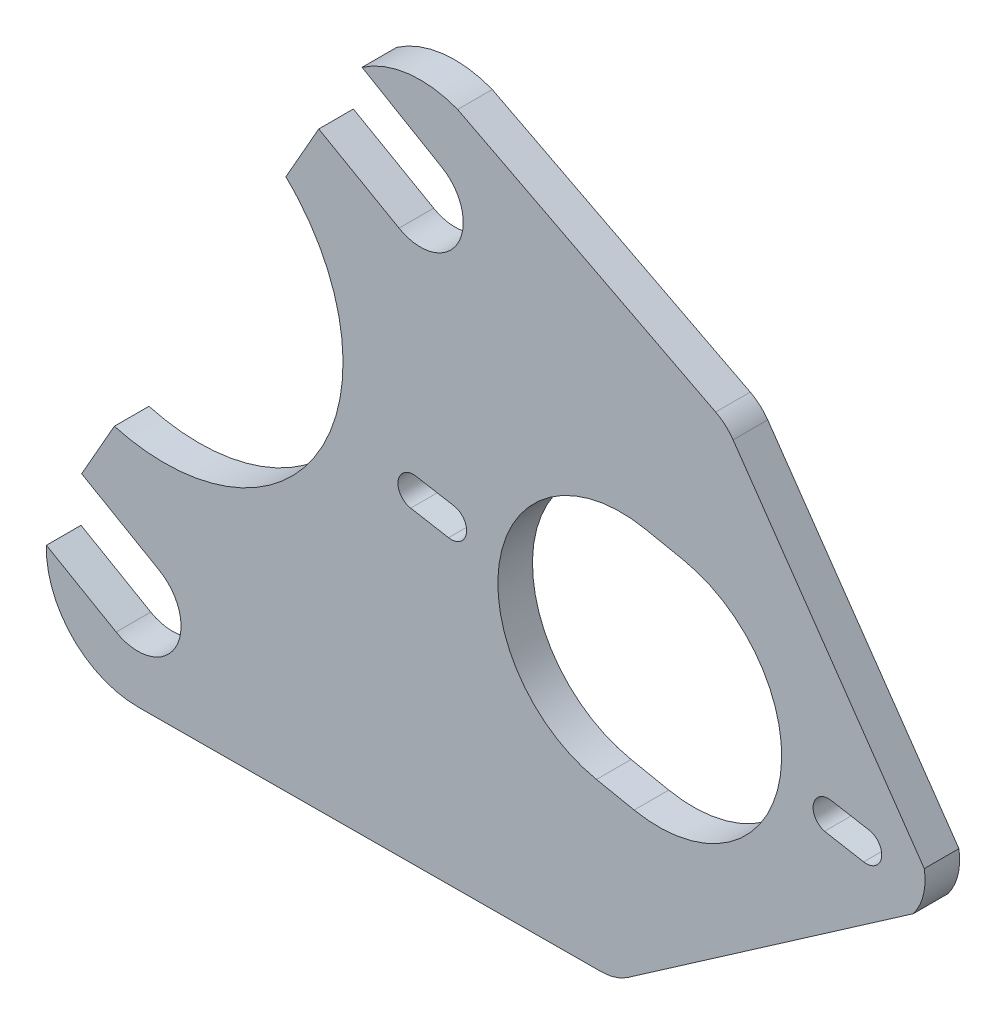
SolidWorks part; units mm, degrees
ref_plane "Front Plane" through (0, 0, 0) normal (0, 0, 1) x (1, 0, 0)
ref_plane "Top Plane" through (0, 0, 0) normal (0, 1, 0) x (1, 0, 0)
ref_plane "Right Plane" through (0, 0, 0) normal (1, 0, 0) x (0, 0, -1)
sketch "Model" plane through (0, 0, 0) normal (0, 0, 1) x (1, 0, 0)
  line L0 (135.7866, 62.5287) -> (131.8474, 63.2232)
  line L1 (59.7829, 35.593) -> (65.7308, 35.6231)
  line L2 (78.5552, 97.0562) -> (86.904, 92.2982)
  line L4 (83.0608, 104.8605) -> (91.3561, 100.0093)
  line L5 (75.135, 91.0384) -> (78.5552, 97.0562)
  line L6 (61.9848, 49.0002) -> (53.897, 53.6704)
  line L7 (53.897, 53.6704) -> (57.2951, 59.6494)
  line L8 (50.2285, 45.3956) -> (57.481, 41.2084)
  line L9 (107.8791, 35.8363) -> (113.8271, 35.8664)
  line L10 (65.7308, 35.6231) -> (107.8791, 35.8363)
  line L11 (116.4435, 77.205) -> (112.5231, 77.9992)
  line L12 (135.2289, 59.3776) -> (131.1616, 60.1004)
  line L13 (92.6109, 70.1416) -> (88.6717, 70.8362)
  line L14 (92.0552, 66.9902) -> (88.116, 67.6848)
  line L15 (111.3606, 52.1146) -> (107.4403, 52.9088)
  line L16 (143.1744, 59.6379) -> (139.0962, 35.8664)
  line L17 (113.8271, 35.8664) -> (139.0962, 35.8664)
  line L18 (92.9995, 106.0361) -> (143.1744, 59.6379)
  arc A0 (57.481, 41.2084) -> (61.9848, 49.0002) centre (59.7329, 45.1043) ccw
  arc A1 (86.904, 92.2982) -> (91.3561, 100.0093) centre (89.13, 96.1538) ccw
  arc A2 (111.3606, 52.1146) -> (116.4435, 77.205) centre (113.9021, 64.6598) ccw
  arc A4 (92.9995, 106.0361) -> (83.0608, 104.8605) centre (89.1296, 96.154) ccw
  arc A5 (50.2285, 45.3956) -> (59.7829, 35.593) centre (59.7348, 45.1036) ccw
  arc A6 (112.5231, 77.9992) -> (107.4403, 52.9088) centre (109.9817, 65.454) ccw
  arc A7 (131.8474, 63.2232) -> (131.4196, 60.0545) centre (131.5696, 61.6475) ccw
  arc A8 (88.729, 70.825) -> (88.116, 67.6848) centre (88.3938, 69.2605) ccw
  arc A9 (92.0552, 66.9902) -> (92.6109, 70.1416) centre (92.3331, 68.5659) ccw
  arc A10 (135.2289, 59.3776) -> (135.7866, 62.5287) centre (135.5088, 60.953) ccw
  ellipse E1 centre (62.0385, 77.7176) end of major axis (78.7041, 68.2458) minor radius 18.6473 (57.2951, 59.6494) -> (75.135, 91.0384) ccw
  point P42 (106.1748, 87.0422)
  point P43 (131.5661, 69.2597)
  point P44 (113.7866, 43.8663)
  point P45 (88.3952, 61.6488)
  point P46 (89.1296, 96.154)
  dimension "D1" = 3.2
  dimension "D2" = 3.2
  dimension "D3" = 3.2
  dimension "D4" = 4
  dimension "D5" = 4
extrude "Boss-Extrude1" add sketch "Model" along normal blind 3.6
sketch "Sketch1" plane through (0, 0, 0) normal (0, 0, -1) x (-1, 0, 0)
  line L0 (-111.0378, 36.9372) -> (-140.869, 57.6203) construction
  line L1 (-111.0378, 36.9372) -> (-140.869, 57.6203)
  line L2 (-140.869, 57.6203) -> (-151.0149, 64.6548)
  line L3 (-151.0149, 64.6548) -> (-139.1687, 25.7481)
  line L4 (-139.1687, 25.7481) -> (-100.6908, 27.009)
  line L5 (-100.6908, 27.009) -> (-96.8976, 27.1333)
  line L6 (-111.0378, 36.9372) -> (-96.8976, 27.1333)
extrude "Cut-Extrude1" cut sketch "Sketch1" against normal blind 10
sketch "Sketch2" plane through (0, 0, 3.6) normal (0, 0, 1) x (1, 0, 0)
  line L1 (143.0928, 59.1621) -> (143.3344, 59.3296)
  line L2 (141.6251, 61.795) -> (143.1638, 59.5758)
  line L3 (120.942, 91.6262) -> (92.9995, 106.0361)
  line L4 (120.942, 91.6262) -> (143.3344, 59.3296)
  line L10 (109.4616, 35.8443) -> (143.0928, 59.1621)
  line L11 (143.0928, 59.1621) -> (143.1744, 59.6379)
  line L12 (143.1744, 59.6379) -> (92.9995, 106.0361)
  line L13 (83.0608, 104.8605) -> (91.3561, 100.0093)
  line L14 (86.904, 92.2982) -> (78.5552, 97.0562)
  line L15 (78.5552, 97.0562) -> (75.135, 91.0384)
  line L16 (57.2951, 59.6494) -> (53.897, 53.6704)
  line L17 (53.897, 53.6704) -> (61.9848, 49.0002)
  line L18 (57.481, 41.2084) -> (50.2285, 45.3956)
  line L19 (59.7829, 35.593) -> (109.4616, 35.8443)
  line L23 (83.0608, 104.8605) -> (91.3561, 100.0093)
  line L24 (86.904, 92.2982) -> (78.5552, 97.0562)
  line L25 (78.5552, 97.0562) -> (75.135, 91.0384)
  line L26 (57.2951, 59.6494) -> (53.897, 53.6704)
  line L27 (53.897, 53.6704) -> (61.9848, 49.0002)
  line L28 (57.481, 41.2084) -> (50.2285, 45.3956)
  line L29 (59.7829, 35.593) -> (109.4616, 35.8443)
  arc A4 (92.9995, 106.0361) -> (83.0608, 104.8605) centre (89.1296, 96.154) ccw
  arc A5 (86.904, 92.2982) -> (91.3561, 100.0093) centre (89.13, 96.1538) ccw
  arc A6 (57.481, 41.2084) -> (61.9848, 49.0002) centre (59.7329, 45.1043) ccw
  arc A7 (50.2285, 45.3956) -> (59.7829, 35.593) centre (59.7348, 45.1036) ccw
  arc A8 (92.9995, 106.0361) -> (83.0608, 104.8605) centre (89.1296, 96.154) ccw
  arc A9 (86.904, 92.2982) -> (91.3561, 100.0093) centre (89.13, 96.1538) ccw
  arc A10 (57.481, 41.2084) -> (61.9848, 49.0002) centre (59.7329, 45.1043) ccw
  arc A11 (50.2285, 45.3956) -> (59.7829, 35.593) centre (59.7348, 45.1036) ccw
  ellipse E1 centre (62.0385, 77.7176) end of major axis (78.7041, 68.2458) minor radius 18.6473 (57.2951, 59.6494) -> (75.135, 91.0384) ccw
  ellipse E2 centre (62.0385, 77.7176) end of major axis (78.7041, 68.2458) minor radius 18.6473 (57.2951, 59.6494) -> (75.135, 91.0384) ccw
  dimension "D1" = 0
extrude "Boss-Extrude2" add sketch "Sketch2" against normal blind 3.6
fillet "Fillet2" radius 5 1 edges at (109.4616, 35.8443, 1.8)
fillet "Fillet3" radius 5 1 edges at (120.942, 91.6262, 1.8)
sketch "Sketch4" plane through (0, 0, 0) normal (0, 0, -1) x (-1, 0, 0)
  line L0 (-139.7366, 65.3566) -> (-145.7221, 59.6101)
  line L1 (-145.7221, 59.6101) -> (-139.7366, 56.5493)
  arc A0 (-139.7366, 65.3566) -> (-139.7366, 56.5493) centre (-135.5088, 60.953) ccw
extrude "Cut-Extrude4" cut sketch "Sketch4" against normal blind 10 contours L0 L1 A0
